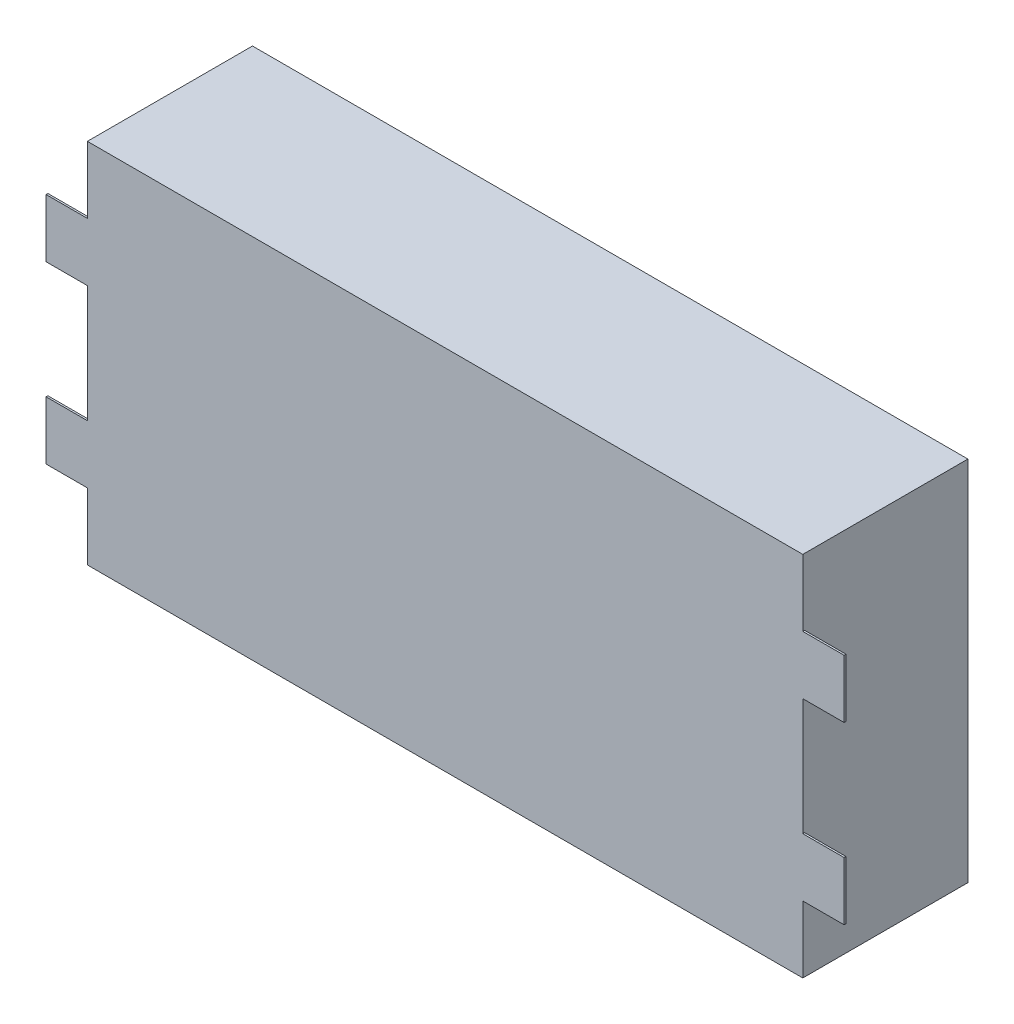
SolidWorks part; units mm, degrees
ref_plane "前视基准面" through (0, 0, 0) normal (0, 0, 1) x (1, 0, 0)
ref_plane "上视基准面" through (0, 0, 0) normal (0, 1, 0) x (1, 0, 0)
ref_plane "右视基准面" through (0, 0, 0) normal (1, 0, 0) x (0, 0, -1)
sketch "草图1" plane through (0, 0, 0) normal (0, 0, 1) x (1, 0, 0)
  line L1 (-39, 20) -> (39, 20)
  line L2 (-39, 20) -> (-39, -20)
  line L3 (-39, -20) -> (39, -20)
  line L4 (39, 20) -> (39, -20)
  line L5 (-39, 20) -> (39, -20) construction
  line L6 (-39, -20) -> (39, 20) construction
  point P0 (0, 0)
  dimension "D1" = 78
  dimension "D2" = 40
extrude "凸台-拉伸1" add sketch "草图1" along normal blind 18
sketch "草图2" plane through (0, 0, 18) normal (0, 0, 1) x (1, 0, 0)
  line L0 (0, 20) -> (0, -20) construction
  line L1 (-39, 0) -> (39, 0) construction
  line L2 (-43.5, -12.725) -> (-43.5, -6.375)
  line L3 (-39, 12.725) -> (-43.5, 12.725)
  line L4 (39, -20) -> (39, 20)
  line L5 (39, 20) -> (-39, 20)
  line L6 (-39, 20) -> (-39, -20)
  line L7 (-39, -20) -> (39, -20)
  line L8 (39, -20) -> (39, 20)
  line L9 (39, 20) -> (-39, 20)
  line L10 (-39, 20) -> (-39, -20)
  line L11 (-39, -20) -> (39, -20)
  line L12 (-39, 12.725) -> (-39, 6.375)
  line L13 (-39, 6.375) -> (-43.5, 6.375)
  line L14 (-43.5, 12.725) -> (-43.5, 6.375)
  line L15 (-39, -6.375) -> (-43.5, -6.375)
  line L16 (-39, -12.725) -> (-39, -6.375)
  line L17 (-39, -12.725) -> (-43.5, -12.725)
  line L18 (39, -12.725) -> (43.5, -12.725)
  line L19 (39, -12.725) -> (39, -6.375)
  line L20 (39, -6.375) -> (43.5, -6.375)
  line L21 (43.5, 12.725) -> (43.5, 6.375)
  line L22 (39, 6.375) -> (43.5, 6.375)
  line L23 (39, 12.725) -> (39, 6.375)
  line L24 (39, 12.725) -> (43.5, 12.725)
  line L25 (43.5, -12.725) -> (43.5, -6.375)
  point P16 (-43.5, 9.55)
  point P17 (-43.5, -9.55)
  point P26 (43.5, -9.55)
  point P27 (43.5, 9.55)
  line M11 (-39, 20) -> (-39, -20)
  dimension "D2" = 4.5
  dimension "D3" = 6.35
  dimension "D4" = 19.1
  dimension "D1" = 0
extrude "凸台-拉伸2" add sketch "草图2" against normal blind 0.2 contours L3 L14 L13 M11 | L17 L15 L2 M11 | L24 L8 L22 L21 | L18 L25 L20 L8
